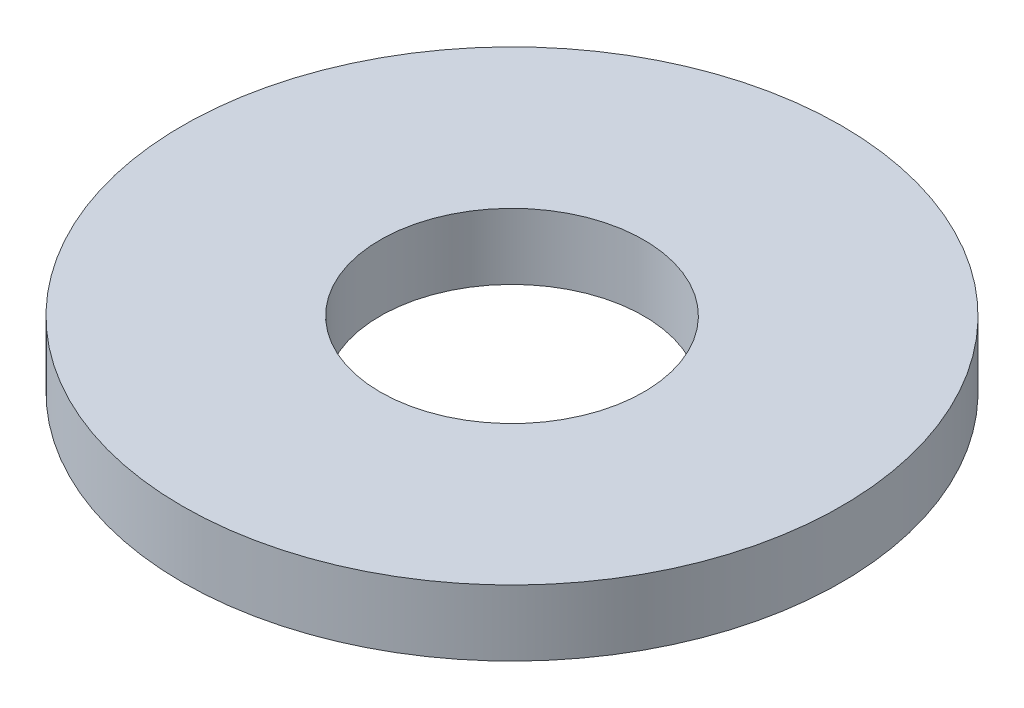
SolidWorks part; units mm, degrees
ref_plane "Front Plane" through (0, 0, 0) normal (0, 0, 1) x (1, 0, 0)
ref_plane "Top Plane" through (0, 0, 0) normal (0, 1, 0) x (1, 0, 0)
ref_plane "Right Plane" through (0, 0, 0) normal (1, 0, 0) x (0, 0, -1)
sketch "Sketch1" plane through (0, 0, 0) normal (0, 1, 0) x (1, 0, 0)
  circle A0 centre (0, 0) radius 2
  circle A1 centre (0, 0) radius 5
  dimension "D1" = 4
  dimension "D2" = 10
extrude "Boss-Extrude1" add sketch "Sketch1" along normal blind 1
